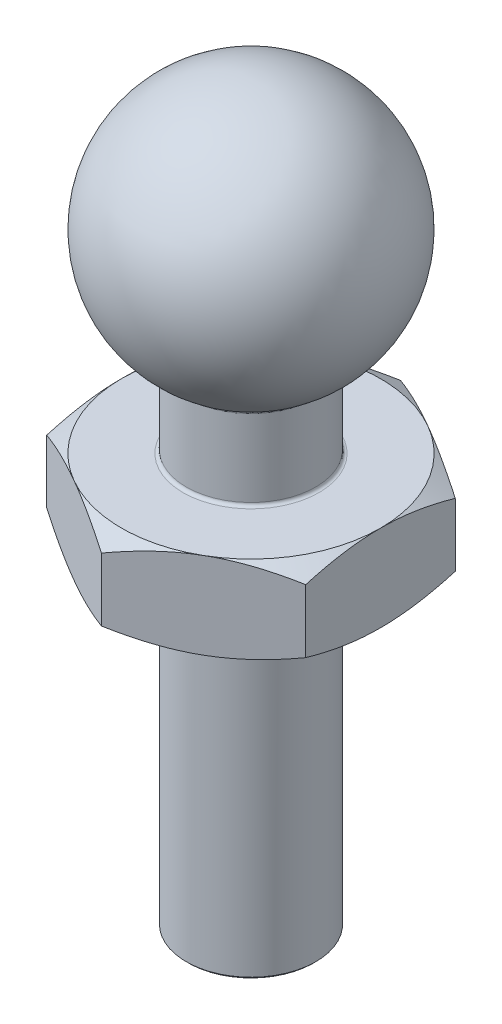
SolidWorks part; units mm, degrees
ref_plane "Front Plane" through (0, 0, 0) normal (0, 0, 1) x (1, 0, 0)
ref_plane "Top Plane" through (0, 0, 0) normal (0, 1, 0) x (1, 0, 0)
ref_plane "Right Plane" through (0, 0, 0) normal (1, 0, 0) x (0, 0, -1)
sketch "Sketch1" plane through (0, 0, 0) normal (0, 0, 1) x (1, 0, 0)
  line L0 (0, 0) -> (0, 11)
  line L1 (0, 11) -> (0, 17)
  line L2 (0, 0) -> (1.5, 0)
  line L3 (1.5, 0) -> (1.5, 11.4019)
  circle A0 centre (0, 14) radius 3 construction
  arc A1 (1.5, 11.4019) -> (0, 17) centre (0, 14) ccw
  dimension "D1" = 6
  dimension "D2" = 11
  dimension "D3" = 1.5
revolve "Revolve2" add sketch "Sketch1" angle 360 about L0
sketch "Sketch3" plane through (0, 0, 0) normal (0, 0, 1) x (1, 0, 0)
  line L0 (-6.0865, 7.5) -> (6.0865, 7.5)
  point P4 (0, 7.5)
  dimension "D1" = 7.5
split line "Split Line3"
chamfer "Chamfer1" distance 0.05 angle 45 1 edges at (0, 0, -1.5)
ref_plane "Plane1" through (0, 7.5, 0) normal (0, 1, 0) x (1, 0, 0)
sketch "Sketch4" plane through (0, 7.5, 0) normal (0, 1, 0) x (1, 0, 0)
  line L1 (0, -3.4641) -> (3, -1.7321)
  line L2 (3, -1.7321) -> (3, 1.7321)
  line L3 (3, 1.7321) -> (0, 3.4641)
  line L4 (0, 3.4641) -> (-3, 1.7321)
  line L5 (-3, 1.7321) -> (-3, -1.7321)
  line L6 (-3, -1.7321) -> (0, -3.4641)
  circle A0 centre (0, 0) radius 1.5
  circle A1 centre (0, 0) radius 3 construction
  circle A2 centre (0, 0) radius 1.5 construction
  dimension "D1" = 6
extrude "Boss-Extrude2" add sketch "Sketch4" along normal blind 2
sketch "Sketch5" plane through (0, 7.5, 0) normal (0, -1, 0) x (1, 0, 0)
  circle A0 centre (0, 0) radius 3 construction
  circle A1 centre (0, 0) radius 3
extrude "Cut-Extrude1" cut sketch "Sketch5" against normal blind 2 draft 60 flip side to cut
sketch "Sketch6" plane through (0, 9.5, 0) normal (0, 1, 0) x (1, 0, 0)
  circle A1 centre (0, 0) radius 3
  circle A2 centre (0, 0) radius 3
  dimension "D1" = 0
extrude "Cut-Extrude2" cut sketch "Sketch6" against normal blind 2 draft 60 flip side to cut
fillet "Fillet1" radius 0.075 2 edges at (0, 11.4019, -1.5) (0, 9.5, 1.5)
